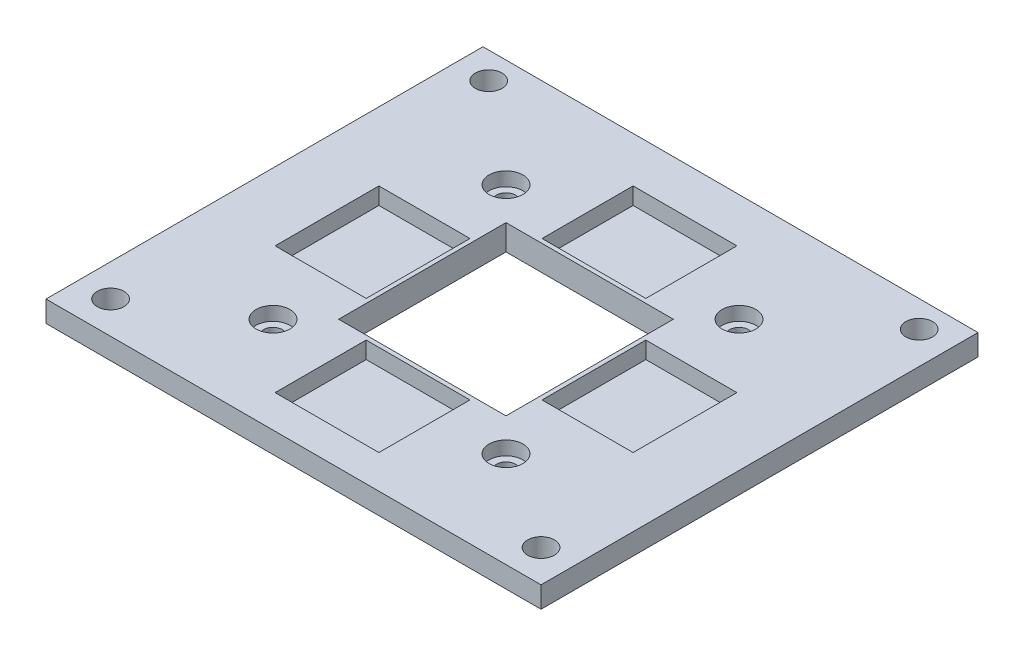
SolidWorks part; units mm, degrees
material "Custom Plastic"
ref_plane "Front Plane" through (0, 0, 0) normal (0, 0, 1) x (1, 0, 0)
ref_plane "Top Plane" through (0, 0, 0) normal (0, 1, 0) x (1, 0, 0)
ref_plane "Right Plane" through (0, 0, 0) normal (1, 0, 0) x (0, 0, -1)
sketch "Sketch1" plane through (0, 0, 0) normal (0, 1, 0) x (1, 0, 0)
  line L1 (-58.42, 52.9821) -> (58.42, 52.9821)
  line L2 (-58.42, 52.9821) -> (-58.42, -50.152)
  line L3 (-58.42, -50.152) -> (58.42, -50.152)
  line L4 (58.42, 52.9821) -> (58.42, -50.152)
  line L5 (-58.42, 52.9821) -> (58.42, -50.152) construction
  line L6 (-58.42, -50.152) -> (58.42, 52.9821) construction
  circle A2 centre (-50.8, 46.711) radius 3.15
  circle A3 centre (50.8, -42.532) radius 3.15
  circle A4 centre (-50.8, -42.532) radius 3.15
  circle A5 centre (50.8, 46.711) radius 3.15
extrude "Boss-Extrude1" add sketch "Sketch1" against normal blind 5
sketch "Sketch10" plane through (0, 0, 0) normal (0, 1, 0) x (1, 0, 0)
  line L1 (-19.75, 19.75) -> (19.75, 19.75)
  line L2 (-19.75, 19.75) -> (-19.75, -19.75)
  line L3 (-19.75, -19.75) -> (19.75, -19.75)
  line L4 (19.75, 19.75) -> (19.75, -19.75)
  line L5 (-19.75, 19.75) -> (19.75, -19.75) construction
  line L6 (-19.75, -19.75) -> (19.75, 19.75) construction
  point P0 (0, 0)
sketch "Sketch12" plane through (0, 0, 0) normal (0, 1, 0) x (1, 0, 0)
  line L1 (-42.5, 69.9875) -> (42.5, 69.9875)
  line L2 (-42.5, 69.9875) -> (-42.5, 46.0125)
  line L3 (-42.5, 46.0125) -> (42.5, 46.0125)
  line L4 (42.5, 69.9875) -> (42.5, 46.0125)
  line L5 (-42.5, 69.9875) -> (42.5, 46.0125) construction
  line L6 (-42.5, 46.0125) -> (42.5, 69.9875) construction
  point P0 (0, 58)
extrude "Boss-Extrude15" add sketch "Sketch12" along normal blind 5 separate body
sketch "Sketch13" plane through (0, 0, 0) normal (0, 1, 0) x (1, 0, 0)
  circle A2 centre (27.5, 27.5) radius 2.25
  circle A3 centre (27.5, -27.5) radius 2.25
  circle A4 centre (-27.5, -27.5) radius 2.25
  circle A5 centre (-27.5, 27.5) radius 2.25
sketch "Sketch17" plane through (0, 0, 0) normal (0, 1, 0) x (1, 0, 0)
  line L1 (-25, 25) -> (25, 25)
  line L2 (-25, 25) -> (-25, -25)
  line L3 (-25, -25) -> (25, -25)
  line L4 (25, 25) -> (25, -25)
  line L5 (-25, 25) -> (25, -25) construction
  line L6 (-25, -25) -> (25, 25) construction
  point P0 (0, 0)
extrude "Boss-Extrude18" add sketch "Sketch17" against normal blind 6 separate body
extrude "Boss-Extrude19" add sketch "Sketch10" along normal mid plane 50 separate body
sketch "Sketch19" plane through (0, 0, 0) normal (0, 1, 0) x (1, 0, 0)
  line L1 (-27.5, 27.5) -> (27.5, 27.5)
  line L2 (-27.5, 27.5) -> (-27.5, -27.5)
  line L3 (-27.5, -27.5) -> (27.5, -27.5)
  line L4 (27.5, 27.5) -> (27.5, -27.5)
  line L5 (-27.5, 27.5) -> (27.5, -27.5) construction
  line L6 (-27.5, -27.5) -> (27.5, 27.5) construction
  point P0 (0, 0)
extrude "Boss-Extrude20" add sketch "Sketch19" against normal blind 11 separate body
combine bodies "Combine1" operation type subtract main body 101 bodies to subtract 136
move or copy body "Body-Move/Copy4" bodies to move or copy 160 copy no translate (0, -6, 0)
combine bodies "Combine4" operation type subtract main body 162 bodies to subtract 164
combine bodies "Combine7" operation type add bodies to combine 167 163
combine bodies "Combine8" operation type subtract main body 168 bodies to subtract 161
sketch "Sketch20" plane through (0, 0, 0) normal (0, 1, 0) x (1, 0, 0)
  circle A2 centre (27.5, 27.5) radius 2.25
  circle A3 centre (27.5, -27.5) radius 2.25
  circle A4 centre (-27.5, -27.5) radius 2.25
  circle A5 centre (-27.5, 27.5) radius 2.25
extrude "Boss-Extrude22" add sketch "Sketch20" along normal mid plane 50 separate body
combine bodies "Combine9" operation type subtract main body 169 bodies to subtract 173 172 171 174
sketch "Sketch21" plane through (0, 0, 0) normal (0, 1, 0) x (1, 0, 0)
  line L1 (-12.25, 42.25) -> (12.25, 42.25)
  line L2 (-12.25, 42.25) -> (-12.25, 20.75)
  line L3 (-12.25, 20.75) -> (12.25, 20.75)
  line L4 (12.25, 42.25) -> (12.25, 20.75)
  line L5 (-12.25, 42.25) -> (12.25, 20.75) construction
  line L6 (-12.25, 20.75) -> (12.25, 42.25) construction
  line L12 (20.75, 12.25) -> (42.25, 12.25)
  line L13 (20.75, 12.25) -> (20.75, -12.25)
  line L14 (20.75, -12.25) -> (42.25, -12.25)
  line L15 (42.25, 12.25) -> (42.25, -12.25)
  line L16 (20.75, 12.25) -> (42.25, -12.25) construction
  line L17 (20.75, -12.25) -> (42.25, 12.25) construction
  line L18 (-42.25, 12.25) -> (-20.75, 12.25)
  line L19 (-42.25, 12.25) -> (-42.25, -12.25)
  line L20 (-42.25, -12.25) -> (-20.75, -12.25)
  line L21 (-20.75, 12.25) -> (-20.75, -12.25)
  line L22 (-42.25, 12.25) -> (-20.75, -12.25) construction
  line L23 (-42.25, -12.25) -> (-20.75, 12.25) construction
  line L24 (-12.25, -20.75) -> (12.25, -20.75)
  line L25 (-12.25, -20.75) -> (-12.25, -42.25)
  line L26 (-12.25, -42.25) -> (12.25, -42.25)
  line L27 (12.25, -20.75) -> (12.25, -42.25)
  line L28 (-12.25, -20.75) -> (12.25, -42.25) construction
  line L29 (-12.25, -42.25) -> (12.25, -20.75) construction
  point P0 (0, 31.5)
  point P11 (31.5, 0)
  point P16 (-31.5, 0)
  point P21 (0, -31.5)
extrude "Boss-Extrude23" add sketch "Sketch21" against normal blind 4 separate body
combine bodies "Combine10" operation type subtract main body 175 bodies to subtract 179 178 177 180
ref_plane "Plane1" through (0, -5, 0) normal (0, -1, 0) x (-1, 0, 0)
sketch "Sketch25" plane through (0, 0, 0) normal (0, 1, 0) x (1, 0, 0)
  circle A0 centre (27.5, 27.5) radius 4
  circle A1 centre (-27.5, 27.5) radius 4
  circle A2 centre (-27.5, -27.5) radius 4
  circle A3 centre (27.5, -27.5) radius 4
extrude "Boss-Extrude24" add sketch "Sketch25" against normal blind 3.25 separate body
combine bodies "Combine11" operation type subtract main body 181 bodies to subtract 195 194 193 196
